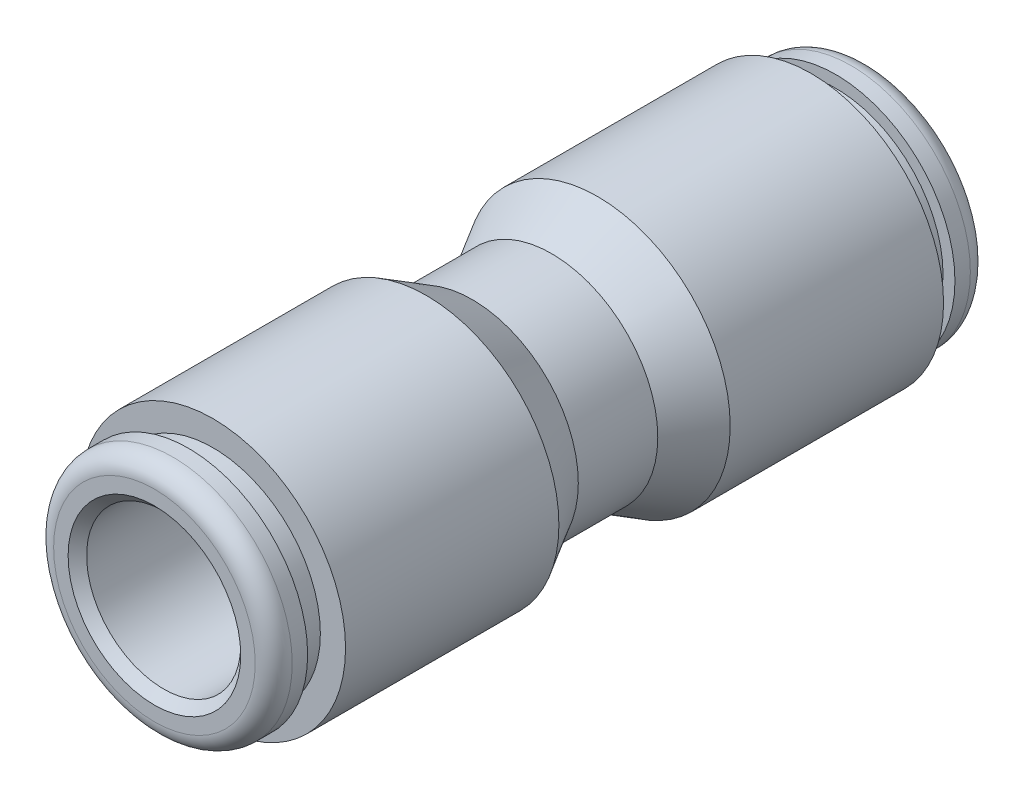
SolidWorks part; units mm, degrees
ref_plane "Front Plane" through (0, 0, 0) normal (0, 0, 1) x (1, 0, 0)
ref_plane "Top Plane" through (0, 0, 0) normal (0, 1, 0) x (1, 0, 0)
ref_plane "Right Plane" through (0, 0, 0) normal (1, 0, 0) x (0, 0, -1)
sketch "Sketch8" plane through (0, 0, 0) normal (1, 0, 0) x (0, 0, -1)
  line L0 (13.335, 4.9149) -> (13.97, 4.9149)
  line L1 (3.5286, 5.461) -> (12.319, 5.461)
  line L2 (0, 4.3688) -> (0, 3.175)
  line L3 (0, 3.175) -> (14.351, 3.175)
  line L4 (14.732, 4.1529) -> (14.732, 3.556)
  line L6 (12.319, 5.461) -> (12.319, 4.4234)
  line L7 (12.319, 4.4234) -> (13.335, 4.4234)
  line L8 (13.335, 4.9149) -> (13.335, 4.4234)
  line L10 (0, 0) -> (14.732, 0) construction
  line L12 (14.351, 3.175) -> (14.732, 3.556)
  line L13 (0, 0) -> (0, 8.6146) construction
  line L14 (0, 4.3688) -> (1.6369, 4.3688)
  line L15 (1.6369, 4.3688) -> (3.5286, 5.461)
  arc A0 (13.97, 4.9149) -> (14.732, 4.1529) centre (13.97, 4.1529) cw
  point P1 (14.732, 3.175)
  point P20 (14.732, 4.9149)
  dimension "D4" = 0.762
  dimension "D1" = 1.397
  dimension "tube od" = 6.35
  dimension "D2" = 1.016
  dimension "D3" = 8.8468
  dimension "D5" = 13.0951
  dimension "G" = 10.922
  dimension "D6" = 9.8298
  dimension "L" = 29.464
  dimension "D9" = 30
  dimension "D10" = 8.7376
revolve "Revolve1" add sketch "Sketch8" angle 360 about L10
sketch "Sketch9" plane through (0, 0, 0) normal (0, 0, 1) x (1, 0, 0)
  circle A0 centre (0, 0) radius 3.175 construction
  circle A1 centre (0, 0) radius 3.175
  circle A2 centre (0, 0) radius 2.413
  dimension "D1" = 0.762
extrude "Extrude1" add sketch "Sketch9" against normal blind 1.016
mirror "Mirror1" about plane through (0, 0, 0) normal (0, 0, 1) of "Revolve1"
equation "\"D3@Sketch8\" = \"D6@Sketch8\"*.9"
equation "\"D6@Sketch8\" = \"G@Sketch8\"*.9"
equation "\"D10@Sketch8\" = \"G@Sketch8\"*.8"
equation "\"D5@Sketch8\" = \"L@Sketch8\"/2.25"
